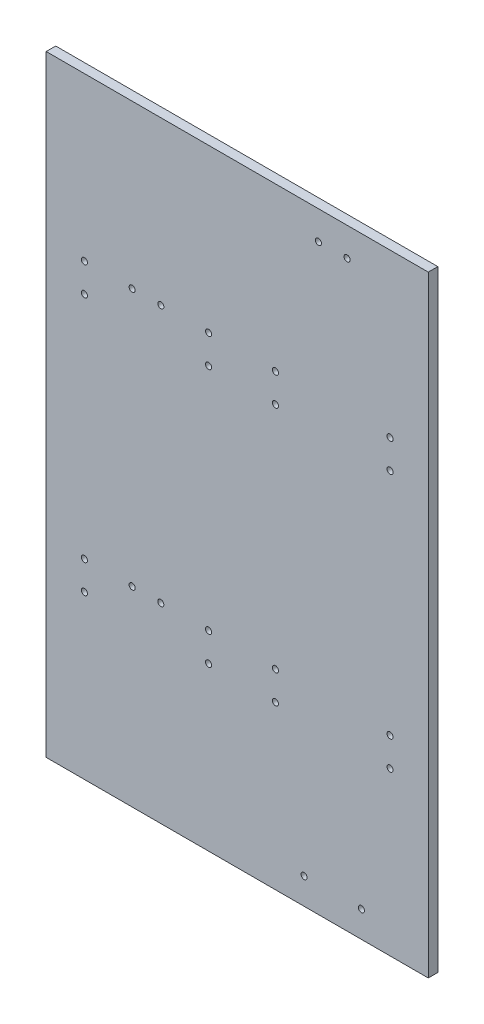
SolidWorks part; units mm, degrees
ref_plane "Front Plane" through (0, 0, 0) normal (0, 0, 1) x (1, 0, 0)
ref_plane "Top Plane" through (0, 0, 0) normal (0, 1, 0) x (1, 0, 0)
ref_plane "Right Plane" through (0, 0, 0) normal (1, 0, 0) x (0, 0, -1)
sketch "Sketch1" plane through (0, 0, 0) normal (0, 0, 1) x (1, 0, 0)
  line L1 (-100, -160) -> (100, -160)
  line L2 (-100, -160) -> (-100, 160)
  line L3 (-100, 160) -> (100, 160)
  line L4 (100, -160) -> (100, 160)
  line L5 (-100, -160) -> (100, 160) construction
  line L6 (-100, 160) -> (100, -160) construction
  point P0 (0, 0)
  dimension "D1" = 320
  dimension "D2" = 200
extrude "Boss-Extrude1" add sketch "Sketch1" along normal blind 5
sketch "Sketch2" plane through (0, 0, 0) normal (0, 0, -1) x (-1, 0, 0)
  line L0 (-95, 0) -> (-80, 0) construction
  line L1 (-95, 160) -> (-95, -160) construction
  line L2 (-80, 0) -> (-80, 60) construction
  line L3 (-80, 60) -> (-80, 75) construction
  line L4 (-80, 0) -> (-50, 0) construction
  line L5 (-50, 0) -> (-50, 25.4966) construction
  circle A0 centre (-80, 75) radius 1.6
  circle A1 centre (-80, 60) radius 1.6
  circle A2 centre (-80, -60) radius 1.6
  circle A3 centre (-80, -75) radius 1.6
  circle A4 centre (-20, -75) radius 1.6
  circle A5 centre (-20, -60) radius 1.6
  circle A6 centre (-20, 60) radius 1.6
  circle A7 centre (-20, 75) radius 1.6
  dimension "D5" = 3.2
  dimension "D6" = 3.2
  dimension "D1" = 15
  dimension "D2" = 60
  dimension "D3" = 15
  dimension "D4" = 30
extrude "Cut-Extrude1" cut sketch "Sketch2" against normal up to next
sketch "Sketch3" plane through (0, 0, 0) normal (0, 0, -1) x (-1, 0, 0)
  line L0 (100, 0) -> (80, 0) construction
  line L3 (100, 160) -> (100, -160) construction
  line L4 (80, 0) -> (80, 60) construction
  line L5 (80, 60) -> (80, 75) construction
  line L6 (80, 0) -> (47.5, 0) construction
  line L7 (47.5, 0) -> (47.5, 17.2306) construction
  circle A0 centre (80, 75) radius 1.6
  circle A1 centre (80, 60) radius 1.6
  circle A2 centre (80, -60) radius 1.6
  circle A3 centre (80, -75) radius 1.6
  circle A4 centre (15, 60) radius 1.6
  circle A5 centre (15, -75) radius 1.6
  circle A6 centre (15, -60) radius 1.6
  circle A7 centre (15, 75) radius 1.6
  dimension "D4" = 3.2
  dimension "D5" = 3.2
  dimension "D1" = 20
  dimension "D2" = 15
  dimension "D3" = 60
  dimension "D6" = 32.5
extrude "Cut-Extrude2" cut sketch "Sketch3" against normal up to next
sketch "Sketch4" plane through (0, 0, 5) normal (0, 0, 1) x (1, 0, 0)
  line L0 (50, 165) -> (50, 145) construction
  line L1 (0, 165) -> (100, 165) construction
  line L2 (50, 145) -> (42.5, 145) construction
  circle A0 centre (42.5, 145) radius 1.6
  circle A1 centre (57.5, 145) radius 1.6
  dimension "D3" = 3.2
  dimension "D1" = 20
  dimension "D2" = 7.5
extrude "Cut-Extrude3" cut sketch "Sketch4" against normal up to next
sketch "Sketch5" plane through (0, 0, 0) normal (0, 0, -1) x (-1, 0, 0)
  line L0 (15, 75) -> (40, 75) construction
  line L1 (40, 75) -> (55, 75) construction
  line L2 (15, -60) -> (40, -60) construction
  line L3 (40, -60) -> (55, -60) construction
  circle A0 centre (40, 75) radius 1.6
  circle A1 centre (55, 75) radius 1.6
  circle A2 centre (40, -60) radius 1.6
  circle A3 centre (55, -60) radius 1.6
  dimension "D3" = 3.2
  dimension "D4" = 3.2
  dimension "D7" = 3.2
  dimension "D8" = 3.2
  dimension "D1" = 25
  dimension "D2" = 15
  dimension "D5" = 25
  dimension "D6" = 15
extrude "Cut-Extrude4" cut sketch "Sketch5" against normal up to next
sketch "Sketch6" plane through (0, 0, 0) normal (0, 0, -1) x (-1, 0, 0)
  line L0 (-95, -160) -> (-95, -146.25) construction
  line L1 (100, -160) -> (-100, -160) construction
  line L2 (-95, 160) -> (-95, -160) construction
  line L3 (-95, -146.25) -> (-65, -146.25) construction
  circle A0 centre (-65, -146.25) radius 1.6
  circle A1 centre (-35, -146.25) radius 1.6
  dimension "D3" = 3.2
  dimension "D1" = 13.75
  dimension "D2" = 30
  dimension "D4" = 2
extrude "Cut-Extrude5" cut sketch "Sketch6" against normal up to next
